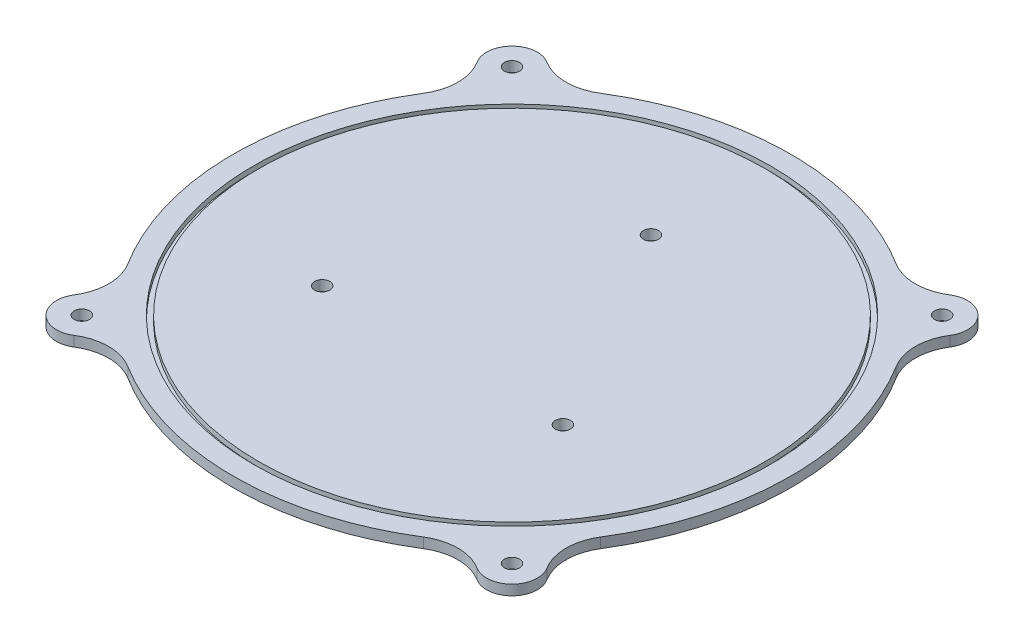
SolidWorks part; units mm, degrees
ref_plane "Front Plane" through (0, 0, 0) normal (0, 0, 1) x (1, 0, 0)
ref_plane "Top Plane" through (0, 0, 0) normal (0, 1, 0) x (1, 0, 0)
ref_plane "Right Plane" through (0, 0, 0) normal (1, 0, 0) x (0, 0, -1)
sketch "Sketch2" plane through (0, 0, 0) normal (0, 1, 0) x (1, 0, 0)
  line L0 (-18.9035, 10.9139) -> (18.9035, 10.9139) construction
  line L1 (-18.9035, 10.9139) -> (0, -21.8279) construction
  line L2 (36.224, 0.9139) -> (17.3205, -31.8279) construction
  line L3 (-36.224, 0.9139) -> (-17.3205, -31.8279) construction
  line L4 (-18.9035, 30.9139) -> (18.9035, 30.9139) construction
  line L5 (18.9035, 10.9139) -> (-49.174, -28.3906) construction
  line L6 (0, -21.8279) -> (0, 37.8367) construction
  line L7 (18.9035, 10.9139) -> (0, -21.8279) construction
  line L8 (-18.9035, 10.9139) -> (24.2933, -14.0257) construction
  line L9 (-18.9035, 10.9139) -> (-51.9615, 30) construction
  line L10 (0, -21.8279) -> (0, -60) construction
  line L11 (18.9035, 10.9139) -> (51.9615, 30) construction
  line L12 (0, 0) -> (-53.378, 53.378) construction
  line L13 (0, 0) -> (74.6655, 0) construction
  arc A0 (-46.6441, 29.1433) -> (-46.6441, -29.1433) centre (0, 0) ccw
  circle A1 centre (0, 0) radius 21.8279 construction
  arc A2 (-39.7649, 46.6592) -> (-46.6592, 39.7649) centre (-42.4264, 42.4264) ccw
  circle A3 centre (-42.4264, 42.4264) radius 1.5
  arc A4 (-46.6441, 29.1433) -> (-46.6592, 39.7649) centre (-55.1248, 34.442) ccw
  arc A5 (-18.9035, 30.9139) -> (-36.224, 0.9139) centre (-18.9035, 10.9139) ccw construction
  circle A6 centre (-23.7412, -13.707) radius 1.5
  arc A7 (-17.3205, -31.8279) -> (17.3205, -31.8279) centre (0, -21.8279) ccw construction
  circle A8 centre (23.7412, -13.707) radius 1.5
  circle A9 centre (0, 27.4139) radius 1.5
  arc A10 (36.224, 0.9139) -> (18.9035, 30.9139) centre (18.9035, 10.9139) ccw construction
  arc A11 (-39.7649, 46.6592) -> (-29.1433, 46.6441) centre (-34.442, 55.1248) ccw
  arc A12 (46.6592, 39.7649) -> (39.7649, 46.6592) centre (42.4264, 42.4264) ccw
  circle A13 centre (42.4264, 42.4264) radius 1.5
  arc A14 (29.1433, 46.6441) -> (39.7649, 46.6592) centre (34.442, 55.1248) ccw
  arc A15 (46.6592, 39.7649) -> (46.6441, 29.1433) centre (55.1248, 34.442) ccw
  arc A16 (39.7649, -46.6592) -> (46.6592, -39.7649) centre (42.4264, -42.4264) ccw
  circle A17 centre (42.4264, -42.4264) radius 1.5
  arc A18 (46.6441, -29.1433) -> (46.6592, -39.7649) centre (55.1248, -34.442) ccw
  arc A19 (39.7649, -46.6592) -> (29.1433, -46.6441) centre (34.442, -55.1248) ccw
  arc A20 (-46.6592, -39.7649) -> (-39.7649, -46.6592) centre (-42.4264, -42.4264) ccw
  circle A21 centre (-42.4264, -42.4264) radius 1.5
  arc A22 (-29.1433, -46.6441) -> (-39.7649, -46.6592) centre (-34.442, -55.1248) ccw
  arc A23 (-46.6592, -39.7649) -> (-46.6441, -29.1433) centre (-55.1248, -34.442) ccw
  arc A24 (29.1433, 46.6441) -> (-29.1433, 46.6441) centre (0, 0) ccw
  arc A25 (46.6441, -29.1433) -> (46.6441, 29.1433) centre (0, 0) ccw
  arc A26 (-29.1433, -46.6441) -> (29.1433, -46.6441) centre (0, 0) ccw
  point P37 (42.9561, 34.3478)
  point P60 (0, 0)
  point P64 (0, 0)
  dimension "D7" = 40
  dimension "D8" = 40
  dimension "D10" = 3
  dimension "D12" = 3
  dimension "D14" = 3
  dimension "D3" = 110
  dimension "D5" = 3
  dimension "D6" = 10
  dimension "D17" = 10
  dimension "D2" = 37.807
  dimension "D9" = 37.807
  dimension "D11" = 3.5
  dimension "D13" = 3.5
  dimension "D15" = 3.5
  dimension "D4" = 135
  dimension "D16" = 60
  dimension "D18" = 4
extrude "Boss-Extrude1" add sketch "Sketch2" along normal blind 2
sketch "Sketch3" plane through (0, 2, 0) normal (0, 1, 0) x (1, 0, 0)
  circle A0 centre (0, 0) radius 51
  circle A1 centre (0, 0) radius 50
  dimension "D1" = 102
  dimension "D2" = 100
extrude "Cut-Extrude1" cut sketch "Sketch3" against normal blind 1
equation "\"thread_dist\"= 3.5"
equation "\"thread_diameter\"= 3"
equation "\"D13@Sketch1\"=\"thread_diameter\""
equation "\"D14@Sketch1\"=\"thread_dist\""
equation "\"D11@Sketch1\"=\"thread_diameter\""
equation "\"D12@Sketch1\"=\"thread_dist\""
equation "\"D8@Sketch1\"=\"thread_diameter\""
equation "\"D10@Sketch1\"=\"thread_dist\""
equation "\"D1@Sketch1\"=\"thread_diameter\""
equation "\"thread_length\"=12"
equation "\"clip_diameter\"= 110"
equation "\"clip_thickness\"= 2"
equation "\"D1@Boss-Extrude1\"=\"clip_thickness\""
equation "\"D3@Sketch2\"=\"clip_diameter\""
equation "\"D16@Sketch2\"=\"clip_diameter\"/2+5"
